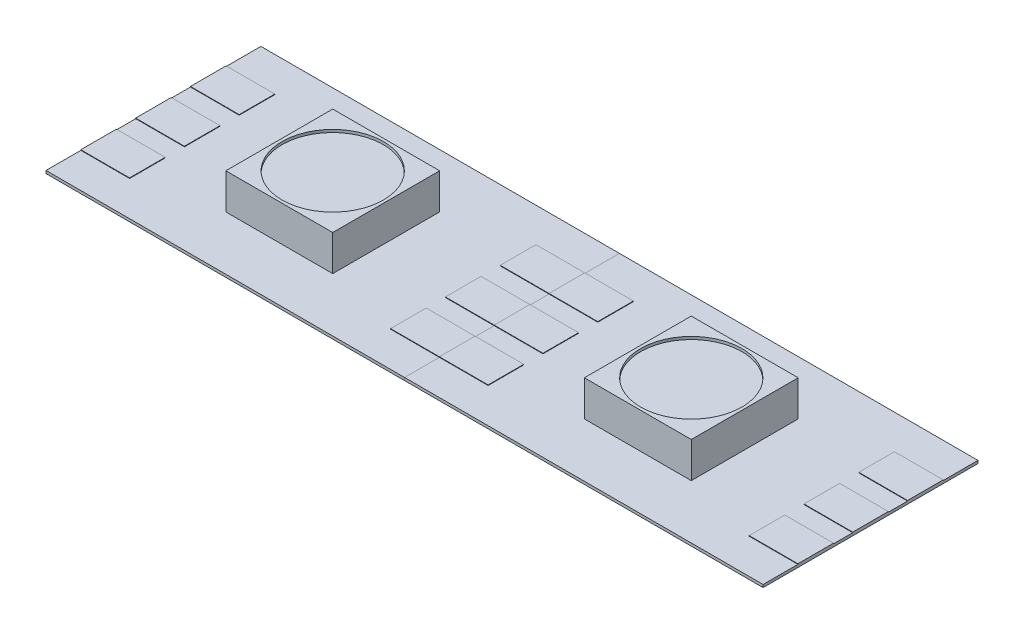
SolidWorks part; units mm, degrees
ref_plane "Front Plane" through (0, 0, 0) normal (0, 0, 1) x (1, 0, 0)
ref_plane "Top Plane" through (0, 0, 0) normal (0, 1, 0) x (1, 0, 0)
ref_plane "Right Plane" through (0, 0, 0) normal (1, 0, 0) x (0, 0, -1)
sketch "Sketch1" plane through (0, 0, 0) normal (0, 1, 0) x (1, 0, 0)
  line L0 (-8.3058, 4.9784) -> (8.3058, -4.9784) construction
  line L1 (-8.3058, 4.9784) -> (8.3058, 4.9784)
  line L2 (-8.3058, 4.9784) -> (-8.3058, -4.9784)
  line L3 (-8.3058, -4.9784) -> (8.3058, -4.9784)
  line L4 (8.3058, 4.9784) -> (8.3058, -4.9784)
  dimension "D1" = 9.9568
  dimension "D2" = 16.6116
extrude "Boss-Extrude1" add sketch "Sketch1" along normal blind 0.127
sketch "Sketch3" plane through (0, 0.127, 0) normal (0, 1, 0) x (1, 0, 0)
  line L0 (-8.3058, 4.9784) -> (8.3058, -4.9784) construction
  line L1 (-2.4765, 2.4765) -> (2.4765, -2.4765) construction
  line L2 (-2.4765, 2.4765) -> (2.4765, 2.4765)
  line L3 (-2.4765, 2.4765) -> (-2.4765, -2.4765)
  line L4 (-2.4765, -2.4765) -> (2.4765, -2.4765)
  line L5 (2.4765, 2.4765) -> (2.4765, -2.4765)
  dimension "D1" = 4.953
extrude "Boss-Extrude3" add sketch "Sketch3" along normal blind 1.651
sketch "Sketch4" plane through (0, 0.127, 0) normal (0, 1, 0) x (1, 0, 0)
  line L0 (-8.3058, 0) -> (8.3058, 0) construction
  line L1 (-8.3058, 4.9784) -> (-8.3058, -4.9784) construction
  line L2 (8.3058, -4.9784) -> (8.3058, 4.9784) construction
  line L3 (-6.047, 0) -> (-8.3058, 0) construction
  line L4 (-8.3058, 0.8255) -> (-6.047, 0.8255)
  line L5 (-8.3058, 0.8255) -> (-8.3058, -0.8255)
  line L6 (-8.3058, -0.8255) -> (-6.047, -0.8255)
  line L7 (-6.047, 0.8255) -> (-6.047, -0.8255)
  line L8 (-8.3058, 3.3655) -> (-6.047, 3.3655)
  line L9 (-6.047, 3.3655) -> (-6.047, 1.7145)
  line L10 (-8.3058, 1.7145) -> (-6.047, 1.7145)
  line L11 (-8.3058, 3.3655) -> (-8.3058, 1.7145)
  line L12 (-6.047, -3.3655) -> (-6.047, -1.7145)
  line L13 (-8.3058, -1.7145) -> (-6.047, -1.7145)
  line L14 (-8.3058, -3.3655) -> (-8.3058, -1.7145)
  line L15 (-8.3058, -3.3655) -> (-6.047, -3.3655)
  line L16 (0, 0) -> (0, -4.9784) construction
  line L17 (-8.3058, -4.9784) -> (8.3058, -4.9784) construction
  line L18 (8.3058, -3.3655) -> (8.3058, -1.7145)
  line L19 (8.3058, -3.3655) -> (6.047, -3.3655)
  line L20 (6.047, -3.3655) -> (6.047, -1.7145)
  line L21 (8.3058, -1.7145) -> (6.047, -1.7145)
  line L22 (8.3058, 0.8255) -> (8.3058, -0.8255)
  line L23 (8.3058, -0.8255) -> (6.047, -0.8255)
  line L24 (6.047, 0.8255) -> (6.047, -0.8255)
  line L25 (8.3058, 0.8255) -> (6.047, 0.8255)
  line L26 (8.3058, 1.7145) -> (6.047, 1.7145)
  line L27 (6.047, 3.3655) -> (6.047, 1.7145)
  line L28 (8.3058, 3.3655) -> (8.3058, 1.7145)
  line L29 (8.3058, 3.3655) -> (6.047, 3.3655)
  dimension "D1" = 1.651
  dimension "D2" = 2
extrude "Boss-Extrude4" add sketch "Sketch4" along normal blind 0.0254
sketch "Sketch5" plane through (0, 1.778, 0) normal (0, 1, 0) x (1, 0, 0)
  circle A0 centre (0, 0) radius 2.3483
extrude "Cut-Extrude1" cut sketch "Sketch5" against normal blind 0.127
pattern_linear "LPattern1" count 2 spacing 16.6116 along (1, 0, 0) of "Boss-Extrude3", "Boss-Extrude4", "Cut-Extrude1", "Boss-Extrude1"
